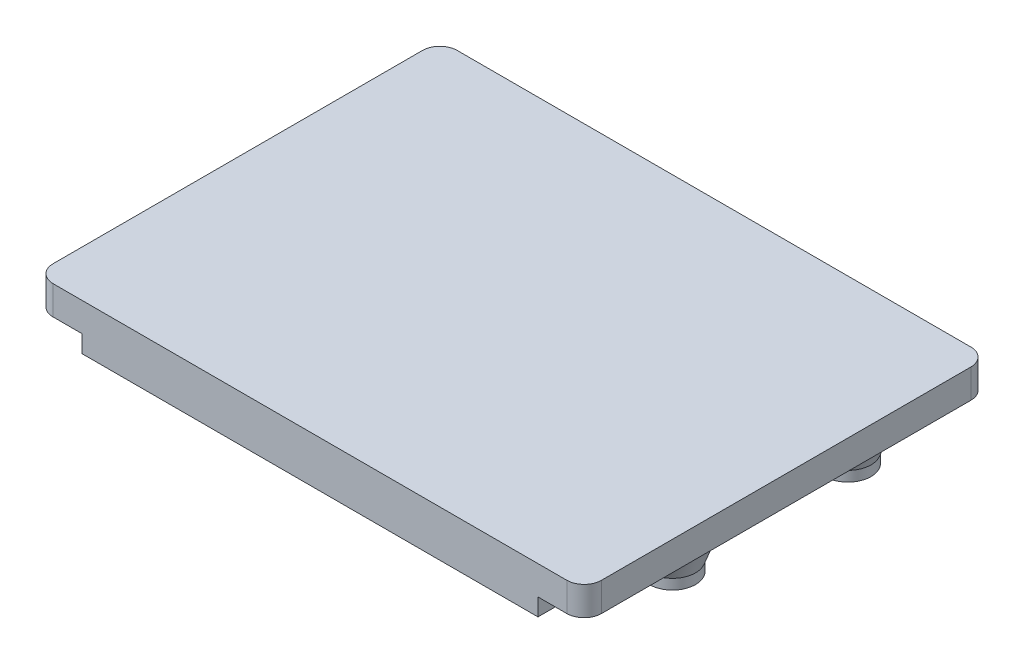
SolidWorks part; units mm, degrees
ref_plane "Plan de face" through (0, 0, 0) normal (0, 0, 1) x (1, 0, 0)
ref_plane "Plan de dessus" through (0, 0, 0) normal (0, 1, 0) x (1, 0, 0)
ref_plane "Plan de droite" through (0, 0, 0) normal (1, 0, 0) x (0, 0, -1)
sketch "Esquisse1" plane through (0, 0, 0) normal (0, 1, 0) x (1, 0, 0)
  line L1 (-47.5, 35) -> (47.5, 35)
  line L2 (-47.5, 35) -> (-47.5, -35)
  line L3 (-47.5, -35) -> (47.5, -35)
  line L4 (47.5, 35) -> (47.5, -35)
  dimension "D1" = 95
  dimension "D2" = 70
  dimension "D3" = 47.5
  dimension "D4" = 35
extrude "Extrusion1" add sketch "Esquisse1" along normal blind 5
sketch "Esquisse2" plane through (0, 0, 0) normal (0, -1, 0) x (1, 0, 0)
  line L0 (-47.5, 35) -> (47.5, 35) construction
  line L2 (-39.5, 35) -> (39.5, 35)
  line L3 (-39.5, 35) -> (-39.5, 30)
  line L4 (-39.5, 30) -> (39.5, 30)
  line L6 (39.5, 35) -> (39.5, 30)
  line L7 (47.5, -35) -> (-47.5, -35) construction
  line L8 (-28.5, -30) -> (29.5, -30)
  line L9 (-28.5, -30) -> (-28.5, -35)
  line L10 (-28.5, -35) -> (29.5, -35)
  line L11 (29.5, -30) -> (29.5, -35)
  line L12 (-47.5, -35) -> (-47.5, 35) construction
  line L13 (-47.5, -5.5) -> (-42.5, -5.5)
  line L14 (-47.5, -5.5) -> (-47.5, -14.5)
  line L16 (-47.5, -14.5) -> (-42.5, -14.5)
  line L17 (-42.5, -5.5) -> (-42.5, -14.5)
  dimension "D1" = 8
  dimension "D2" = 79
  dimension "D3" = 20.5
  dimension "D4" = 9
  dimension "D5" = 19
  dimension "D6" = 58
  dimension "D7" = 5
  dimension "D8" = 5
  dimension "D9" = 5
extrude "Extrusion2" add sketch "Esquisse2" along normal blind 3
sketch "Esquisse3" plane through (0, 0, 0) normal (0, -1, 0) x (1, 0, 0)
  line L0 (-47.5, -35) -> (-47.5, -14.5) construction
  line L1 (-47.5, 9.5) -> (-42.5, 9.5)
  line L2 (-47.5, 9.5) -> (-47.5, 0.5)
  line L3 (-47.5, 0.5) -> (-42.5, 0.5)
  line L4 (-42.5, 9.5) -> (-42.5, 0.5)
  line L7 (-42.5, -5.5) -> (-47.5, -5.5) construction
  dimension "D1" = 5
  dimension "D2" = 6
  dimension "D3" = 9
extrude "Extrusion3" add sketch "Esquisse3" along normal blind 5
fillet "Congé1" radius 3 4 edges at (47.5, 2.5, -35) (-47.5, 2.5, -35) (-47.5, 2.5, 35) (47.5, 2.5, 35)
sketch "Esquisse5" plane through (0, 0, 0) normal (0, -1, 0) x (1, 0, 0)
  line L0 (47.5, 32) -> (47.5, -32) construction
  line L1 (39.5, 35) -> (-39.5, 35) construction
  line L2 (44.5, -35) -> (29.5, -35) construction
  line L3 (-47.5, -32) -> (-47.5, -14.5) construction
  line L4 (-47.5, 9.5) -> (-47.5, 32) construction
  line L5 (-28.5, -35) -> (-44.5, -35) construction
  circle A0 centre (-25.5, 10.5) radius 1.6
  circle A1 centre (37.3, 9.5) radius 1.6
  circle A2 centre (36.3, -21.9) radius 1.6
  circle A3 centre (-36.5, -23.5) radius 1.6
  circle A4 centre (-25.5, 10.5) radius 4
  circle A5 centre (37.3, 9.5) radius 4
  circle A6 centre (36.3, -21.9) radius 4
  circle A7 centre (-36.5, -23.5) radius 4
  point P15 (-47.5, -23.25)
  dimension "D9" = 3.2
  dimension "D10" = 3.2
  dimension "D11" = 3.2
  dimension "D12" = 3.2
  dimension "D13" = 8
  dimension "D14" = 8
  dimension "D15" = 8
  dimension "D16" = 8
  dimension "D1" = 10.2
  dimension "D2" = 25.5
  dimension "D3" = 13.1
  dimension "D4" = 11.2
  dimension "D5" = 11
  dimension "D6" = 22
  dimension "D7" = 11.5
  dimension "D8" = 24.5
extrude "Extrusion4" add sketch "Esquisse5" along normal blind 10
chamfer "Chanfrein1" distance 3 angle 70 4 edges at (-25.5, 0, 14.5) (-36.5, 0, -19.5) (36.3, 0, -17.9) (37.3, 0, 13.5)
